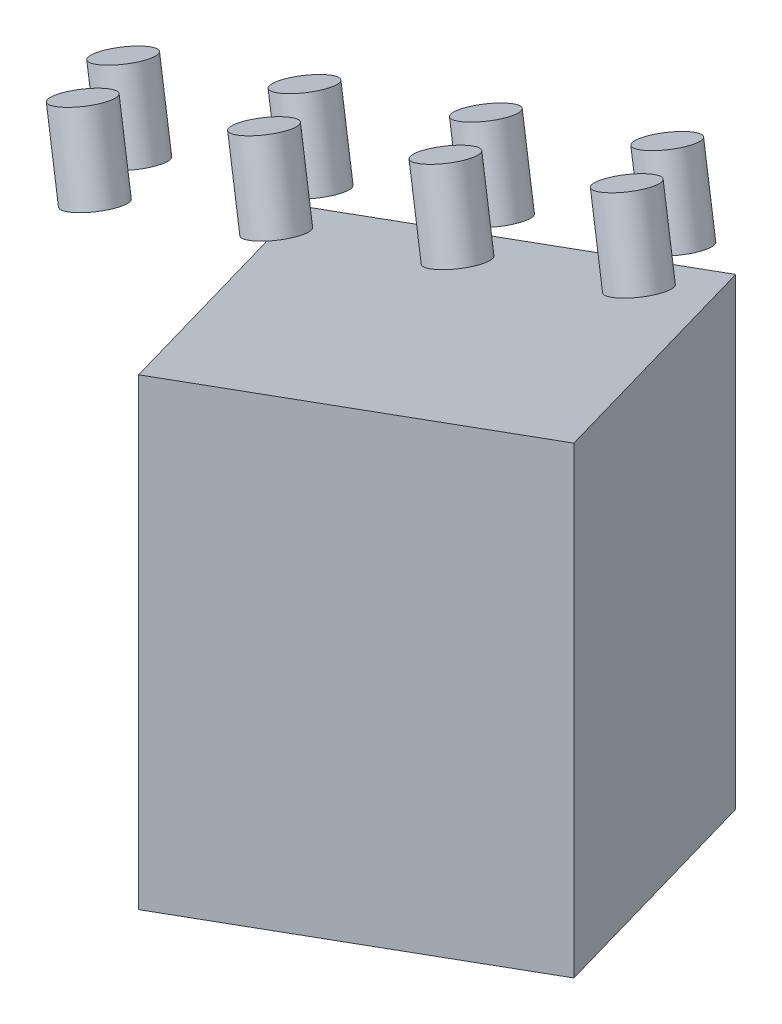
SolidWorks part; units mm, degrees
ref_plane "Ebene vorne" through (0, 0, 0) normal (0, 0, 1) x (1, 0, 0)
ref_plane "Ebene oben" through (0, 0, 0) normal (0, 1, 0) x (1, 0, 0)
ref_plane "Ebene rechts" through (0, 0, 0) normal (1, 0, 0) x (0, 0, -1)
sketch "SK Grundriss" plane through (0, 0, 0) normal (0, 0, 1) x (1, 0, 0)
  line L0 (0, 0) -> (0, 60)
  line L1 (0, 0) -> (56.3816, 20.5212)
  line L2 (0, 60) -> (56.3816, 80.5212)
  line L3 (56.3816, 20.5212) -> (56.3816, 80.5212)
  dimension "Winkel" = 70
  dimension "Seitenlänge" = 60
sketch "SK Schnittebene" plane through (0, 0, 0) normal (1, 0, 0) x (0, 0, -1)
  line L0 (0, 0) -> (-60, 0)
  dimension "D1" = 60
ref_plane "Ebene1" through (0, 0, 0) normal (-0.5736, 0.8192, 0) x (0, 0, 1)
sketch "SK Pfad" plane through (0, 0, 0) normal (-0.5736, 0.8192, 0) x (0, 0, 1)
  line L0 (0, 0) -> (60, 0) construction
  line L1 (0, 0) -> (49.1491, 34.4146)
  dimension "Länge egal" = 60
  dimension "Winkel" = 35
  dimension "Länge" = 60
sweep "Austragung1" add profiles "SK Grundriss" path "SK Pfad"
sketch "Skizze1" plane through (-18.6704, 51.2966, -9.8929) normal (-0.3365, 0.9246, -0.1783) x (0.9417, 0.3304, -0.0637)
  circle A0 centre (74.2954, -22.475) radius 3.3584
extrude "Aufsatz-Linear austragen1" add sketch "Skizze1" along normal blind 10 separate body
pattern_linear "Lineares Muster2" count 4 spacing 25 along (-0.9397, -0.342, 0) count 2 spacing 15 along (-0.4698, -0.329, -0.8192) of "Aufsatz-Linear austragen1"
equation "\"Anzahlx\"= 3"
